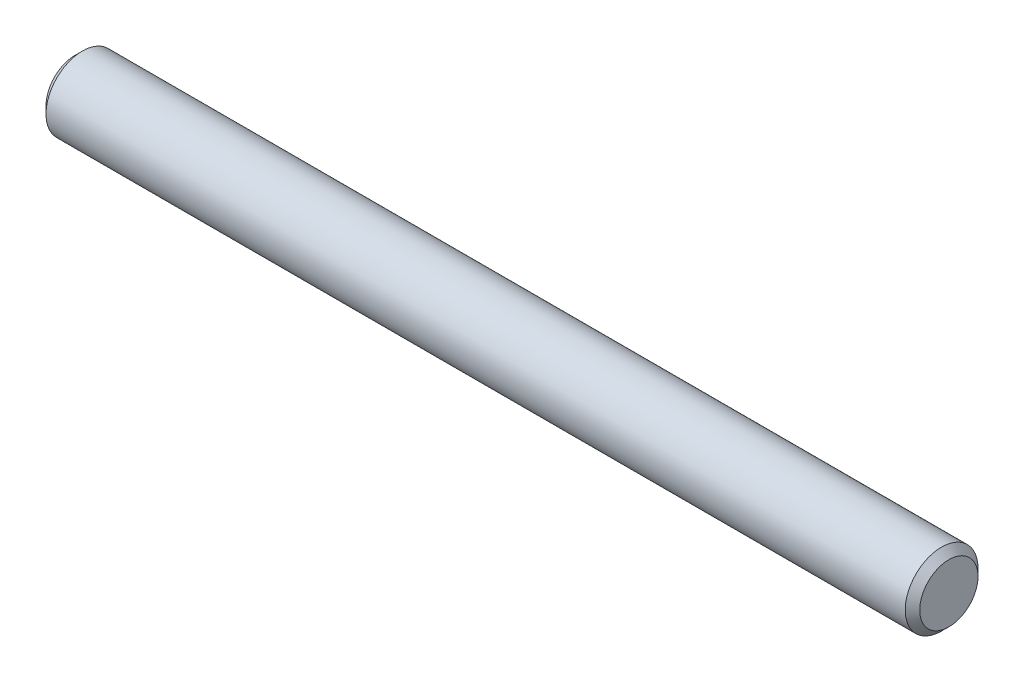
SolidWorks part; units mm, degrees
ref_plane "Front Plane" through (0, 0, 0) normal (0, 0, 1) x (1, 0, 0)
ref_plane "Top Plane" through (0, 0, 0) normal (0, 1, 0) x (1, 0, 0)
ref_plane "Right Plane" through (0, 0, 0) normal (1, 0, 0) x (0, 0, -1)
sketch "Sketch1" plane through (0, 0, 0) normal (0, 0, 1) x (1, 0, 0)
  line L0 (-9.525, 0) -> (9.525, 0) construction
  line L1 (-9.525, 0.7937) -> (-9.525, -0.7937) construction
  line L2 (9.525, 0.7937) -> (9.525, -0.7937) construction
  dimension "Diameter" = 1.5875
  dimension "Length" = 19.05
sketch "Sketch2" plane through (0, 0, 0) normal (1, 0, 0) x (0, 0, -1)
  circle A0 centre (0, 0) radius 0.7937
extrude "Extrude1" add sketch "Sketch2" against normal up to vertex (9.525 mm away) and the other way up to vertex (9.525 mm away) up to point (-9.525, 0, 0) other way up to point (9.525, 0, 0)
chamfer "Chamfer1" distance 0.1588 angle 45 2 edges at (9.525, 0, -0.7937) (-9.525, 0, -0.7937)
equation "\"D1@Chamfer1\" = \"Diameter@Sketch1\"*.1"
